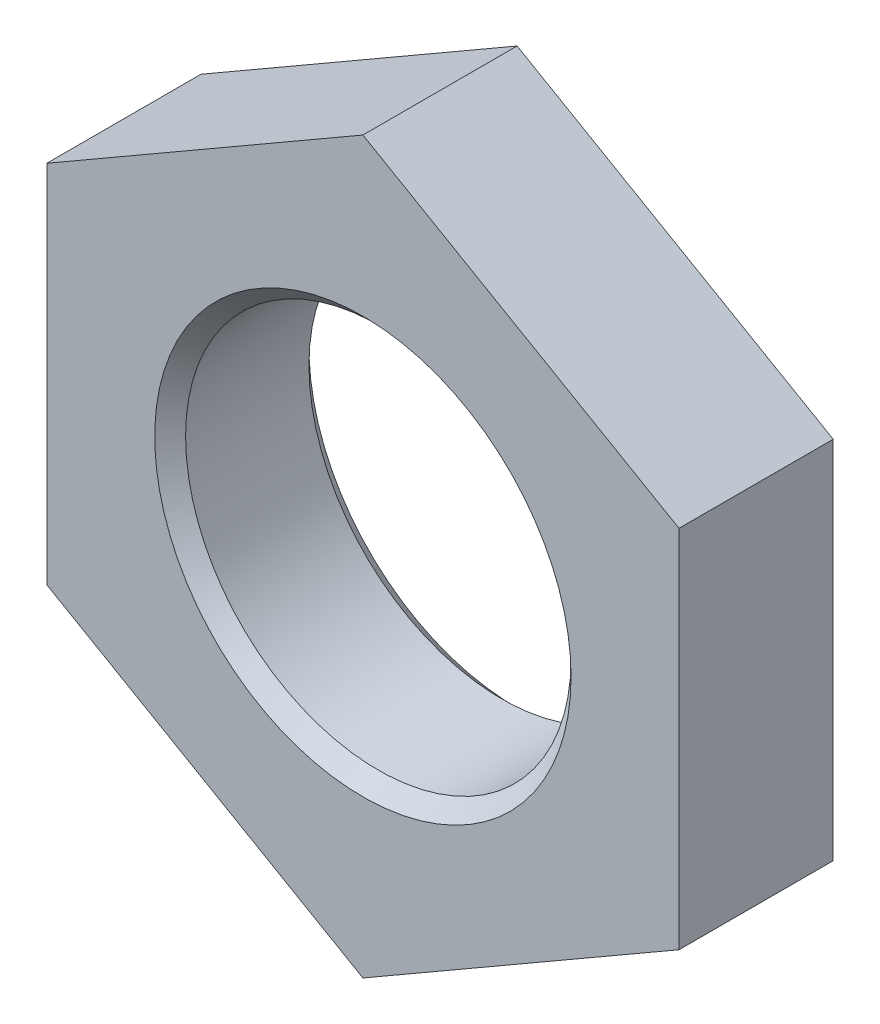
SolidWorks part; units mm, degrees
ref_plane "Front Plane" through (0, 0, 0) normal (0, 0, 1) x (1, 0, 0)
ref_plane "Top Plane" through (0, 0, 0) normal (0, 1, 0) x (1, 0, 0)
ref_plane "Right Plane" through (0, 0, 0) normal (1, 0, 0) x (0, 0, -1)
sketch "Sketch1" plane through (0, 0, 0) normal (0, 0, 1) x (1, 0, 0)
  line L1 (0, 4.7343) -> (-4.1, 2.3671)
  line L2 (-4.1, 2.3671) -> (-4.1, -2.3671)
  line L3 (-4.1, -2.3671) -> (0, -4.7343)
  line L4 (0, -4.7343) -> (4.1, -2.3671)
  line L5 (4.1, -2.3671) -> (4.1, 2.3671)
  line L6 (4.1, 2.3671) -> (0, 4.7343)
  circle A0 centre (0, 0) radius 4.1 construction
  circle A1 centre (0, 0) radius 2.5
  dimension "D2" = 5
  dimension "D1" = 8.2
extrude "Boss-Extrude1" add sketch "Sketch1" along normal blind 2
chamfer "Chamfer1" distance 0.2 angle 45 2 edges at (2.5, 0, 0) (2.5, 0, 2)
